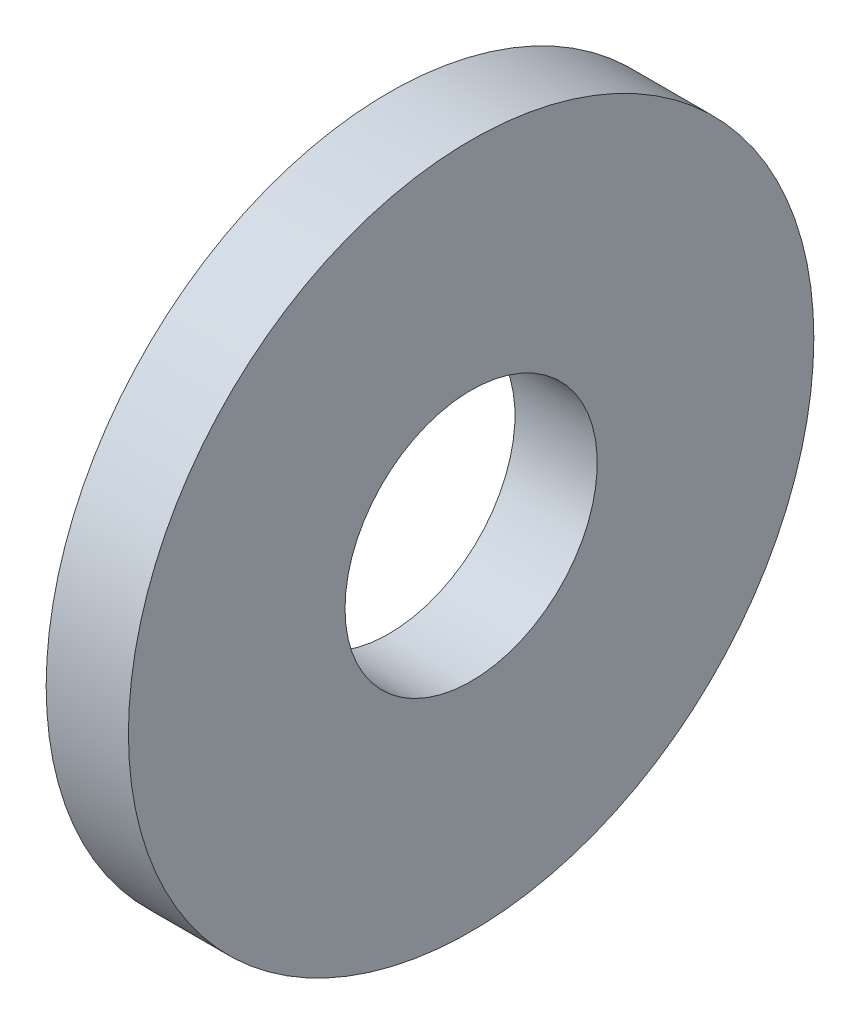
SolidWorks part; units mm, degrees
ref_plane "Plane1" through (0, 0, 0) normal (0, 0, 1) x (1, 0, 0)
ref_plane "Plane2" through (0, 0, 0) normal (0, 1, 0) x (1, 0, 0)
ref_plane "Plane3" through (0, 0, 0) normal (1, 0, 0) x (0, 0, -1)
sketch "Sketch1" plane through (0, 0, 0) normal (0, 0, 1) x (1, 0, 0)
  line L0 (-34.925, 0) -> (9.525, 0) construction
  line L1 (0, 1.84) -> (0, 5)
  line L2 (0, 5) -> (-1.2, 5)
  line L3 (-1.2, 5) -> (-1.2, 1.84)
  line L4 (-1.2, 1.84) -> (0, 1.84)
  dimension "Thickness" = 1.2
  dimension "Inside_dia" = 3.68
  dimension "Outside_dia" = 10
revolve "Base-Revolve" add sketch "Sketch1" angle 360 about L0
